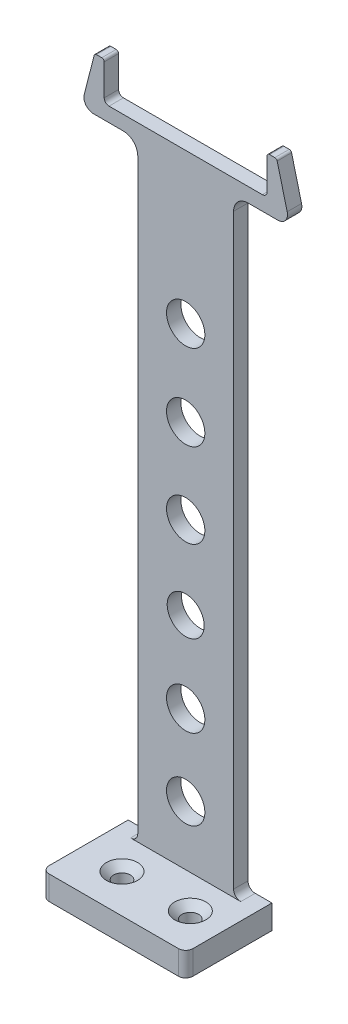
SolidWorks part; units mm, degrees
ref_plane "Спереди" through (0, 0, 0) normal (0, 0, 1) x (1, 0, 0)
ref_plane "Сверху" through (0, 0, 0) normal (0, 1, 0) x (1, 0, 0)
ref_plane "Справа" through (0, 0, 0) normal (1, 0, 0) x (0, 0, -1)
sketch "Sketch1" plane through (0, 0, 0) normal (0, 0, 1) x (1, 0, 0)
  line L0 (0, 0) -> (20, 0)
  line L1 (20, 0) -> (20, 124)
  line L2 (20, 130) -> (0, 130)
  line L3 (0, 124) -> (0, 0)
  line L4 (0, 0) -> (-5, 0)
  line L5 (-5, 0) -> (-5, -5)
  line L6 (-5, -5) -> (25, -5)
  line L7 (25, -5) -> (25, 0)
  line L8 (25, 0) -> (20, 0)
  line L9 (10, 130) -> (-6, 130)
  line L10 (10, 130) -> (26, 130)
  line L11 (27, 131) -> (27, 137.5)
  line L12 (27.5, 138) -> (28.612, 138)
  line L13 (20, 130) -> (20, 127)
  line L14 (29.2412, 127) -> (23, 127)
  line L16 (29.0963, 137.6241) -> (31.1786, 129.4964)
  line L17 (-9.2412, 127) -> (-3, 127)
  line L18 (-9.0963, 137.6241) -> (-11.1786, 129.4964)
  line L19 (-7.5, 138) -> (-8.612, 138)
  line L20 (-7, 131) -> (-7, 137.5)
  arc A0 (31.1786, 129.4964) -> (29.2412, 127) centre (29.2412, 129) cw
  arc A1 (27.5, 138) -> (27, 137.5) centre (27.5, 137.5) ccw
  arc A2 (28.612, 138) -> (29.0963, 137.6241) centre (28.612, 137.5) cw
  arc A3 (-11.1786, 129.4964) -> (-9.2412, 127) centre (-9.2412, 129) ccw
  arc A4 (-8.612, 138) -> (-9.0963, 137.6241) centre (-8.612, 137.5) ccw
  arc A5 (-7.5, 138) -> (-7, 137.5) centre (-7.5, 137.5) cw
  arc A6 (26, 130) -> (27, 131) centre (26, 131) ccw
  arc A7 (-6, 130) -> (-7, 131) centre (-6, 131) cw
  arc A8 (20, 124) -> (23, 127) centre (23, 124) cw
  arc A9 (0, 124) -> (-3, 127) centre (-3, 124) ccw
  dimension "D1" = 2
  dimension "D2" = 0.5
  dimension "D3" = 1
  dimension "D4" = 3
extrude "Boss-Extrude1" add sketch "Sketch1" along normal blind 3
sketch "Sketch2" plane through (0, 0, 3) normal (0, 0, 1) x (1, 0, 0)
  line L1 (-5, 0) -> (25, 0)
  line L2 (-5, 0) -> (-5, -5)
  line L3 (-5, -5) -> (25, -5)
  line L4 (25, 0) -> (25, -5)
extrude "Boss-Extrude2" add sketch "Sketch2" along normal blind 15
sketch "Sketch3" plane through (0, 0, 0) normal (0, 1, 0) x (1, 0, 0)
  circle A0 centre (17.9166, -9.9486) radius 1.75
  circle A1 centre (3.6597, -9.9486) radius 1.75
extrude "Cut-Extrude1" cut sketch "Sketch3" against normal through all contours A1 | A0
chamfer "Chamfer1" distance 1.5 angle 45 2 edges at (17.9166, 0, 11.6986) (3.6597, 0, 11.6986)
fillet "Fillet1" radius 1.5 4 edges at (20, 0, 1.5) (0, 0, 1.5) (-5, -2.5, 18) (25, -2.5, 18)
sketch "Sketch4" plane through (0, 0, 0) normal (0, 0, -1) x (-1, 0, 0)
  circle A0 centre (-10, 12.3487) radius 4
  circle A1 centre (-10, 63.2638) radius 4
  circle A2 centre (-10, 29.1172) radius 4
  circle A3 centre (-10, 98.6683) radius 4
  circle A4 centre (-10, 46.0108) radius 3.8646
  circle A7 centre (-10, 80.8762) radius 4
extrude "Cut-Extrude2" cut sketch "Sketch4" against normal blind 15
